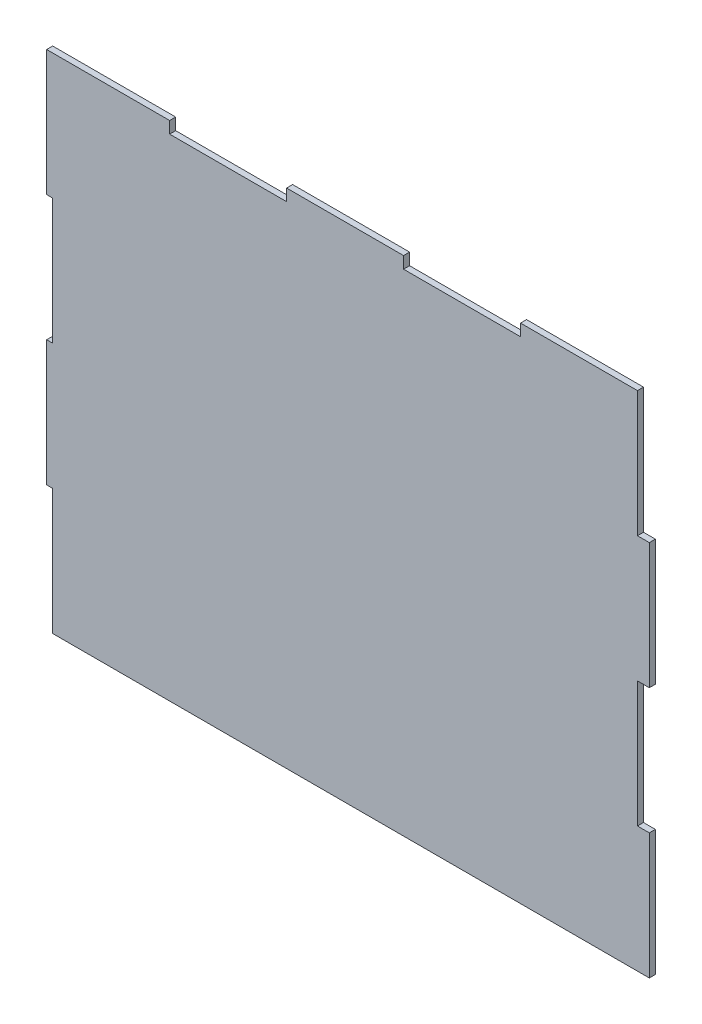
SolidWorks part; units mm, degrees
material "Acrylic (Medium-high impact)"
ref_plane "Front Plane" through (0, 0, 0) normal (0, 0, 1) x (1, 0, 0)
ref_plane "Top Plane" through (0, 0, 0) normal (0, 1, 0) x (1, 0, 0)
ref_plane "Right Plane" through (0, 0, 0) normal (1, 0, 0) x (0, 0, -1)
sketch "Sketch1" plane through (0, 0, 0) normal (0, 0, 1) x (1, 0, 0)
  line L2 (-3.048, 63.5) -> (-3.048, 127)
  line L3 (-3.048, 253.9817) -> (59.0804, 253.9817)
  line L4 (301.3964, 0) -> (301.3964, 63.5)
  line L7 (0, 0) -> (0, 63.5)
  line L8 (0, 63.5) -> (-3.048, 63.5)
  line L9 (0, 127) -> (-3.048, 127)
  line L10 (0, 127) -> (0, 190.5)
  line L11 (0, 190.5) -> (-3.048, 190.5)
  line L12 (-3.048, 190.5) -> (-3.048, 253.9817)
  line L13 (0, 0) -> (301.3964, 0)
  line L14 (59.0804, 253.9817) -> (59.0804, 248.0127)
  line L15 (59.0804, 248.0127) -> (118.1608, 248.0127)
  line L16 (118.1608, 248.0127) -> (118.1608, 253.9817)
  line L17 (177.2412, 253.9817) -> (177.2412, 248.0127)
  line L18 (177.2412, 248.0127) -> (236.3216, 248.0127)
  line L19 (236.3216, 248.0127) -> (236.3216, 253.9817)
  line L20 (118.1608, 253.9817) -> (177.2412, 253.9817)
  line L21 (236.3216, 253.9817) -> (295.402, 253.9817)
  line L22 (301.3964, 63.5) -> (295.402, 63.5)
  line L23 (295.402, 63.5) -> (295.402, 126.9817)
  line L24 (295.402, 126.9817) -> (301.3964, 126.9817)
  line L25 (301.3964, 190.4817) -> (295.402, 190.4817)
  line L26 (295.402, 190.4817) -> (295.402, 253.9817)
  line L29 (301.3964, 126.9817) -> (301.3964, 190.4817)
  dimension "D1" = 254
  dimension "D2" = 298.45
  dimension "D3" = 59.0804
  dimension "D6" = 63.5
  dimension "D7" = 3.048
  dimension "D8" = 5.969
  dimension "D10" = 5.9944
extrude "Boss-Extrude1" add sketch "Sketch1" along normal blind 3.048
sketch "Sketch2" plane through (0, 0, 3.048) normal (0, 0, 1) x (1, 0, 0)
  line L0 (0, 0) -> (301.3964, 0) construction
  line L1 (301.3964, 0) -> (301.3964, 63.5) construction
  circle A0 centre (275.9964, 50.8) radius 2.921
  dimension "D1" = 5.842
  dimension "D2" = 50.8
  dimension "D3" = 25.4
extrude "Cut-Extrude1" [suppressed] cut sketch "Sketch2" against normal up to next
